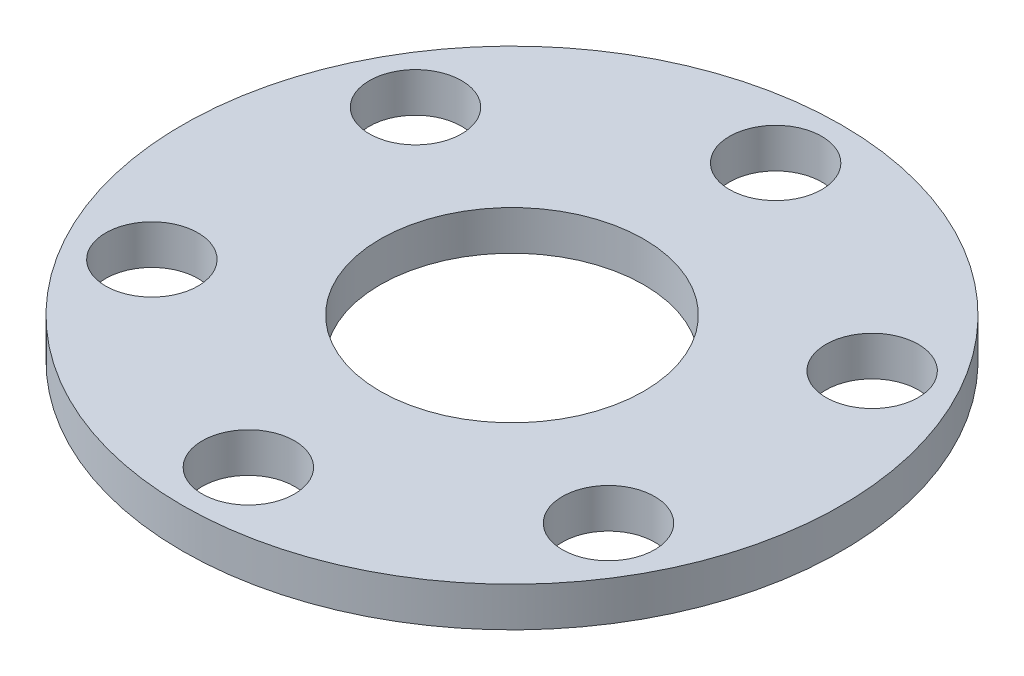
SolidWorks part; units mm, degrees
material "Stainless Steel (ferritic)"
ref_plane "Front Plane" through (0, 0, 0) normal (0, 0, 1) x (1, 0, 0)
ref_plane "Top Plane" through (0, 0, 0) normal (0, 1, 0) x (1, 0, 0)
ref_plane "Right Plane" through (0, 0, 0) normal (1, 0, 0) x (0, 0, -1)
sketch "Sketch1" plane through (0, 0, 0) normal (0, 1, 0) x (1, 0, 0)
  circle A0 centre (0, 0) radius 10 construction
  circle A1 centre (0, 0) radius 12.5
  circle A2 centre (0, 0) radius 5
  dimension "D1" = 20
  dimension "D3" = 25
  dimension "D2" = 5
extrude "Boss-Extrude1" add sketch "Sketch1" along normal blind 1.5
sketch "Sketch2" plane through (0, 0, 0) normal (0, 1, 0) x (1, 0, 0)
  circle A0 centre (0, 0) radius 10 construction
  circle A1 centre (0, 10) radius 1.75
  dimension "D1" = 3.5
  dimension "D2" = 20
extrude "Cut-Extrude1" cut sketch "Sketch2" along normal through all
pattern_circular "CirPattern1" count 6 over 360 about axis through (0, 0, 0) along (0, 1, 0) of "Cut-Extrude1"
equation "\"motor_shaft_mounting_hole_circle_diameter\"= 20mm"
equation "\"ring_width\"= 10mm"
equation "\"material_thickness\"= 1.5mm"
equation "\"D1@Sketch1\"=\"motor_shaft_mounting_hole_circle_diameter\""
equation "\"D2@Sketch1\"=\"ring_width\"/2"
equation "\"D1@Boss-Extrude1\"=\"material_thickness\""
equation "\"D2@Sketch2\"=\"motor_shaft_mounting_hole_circle_diameter\""
